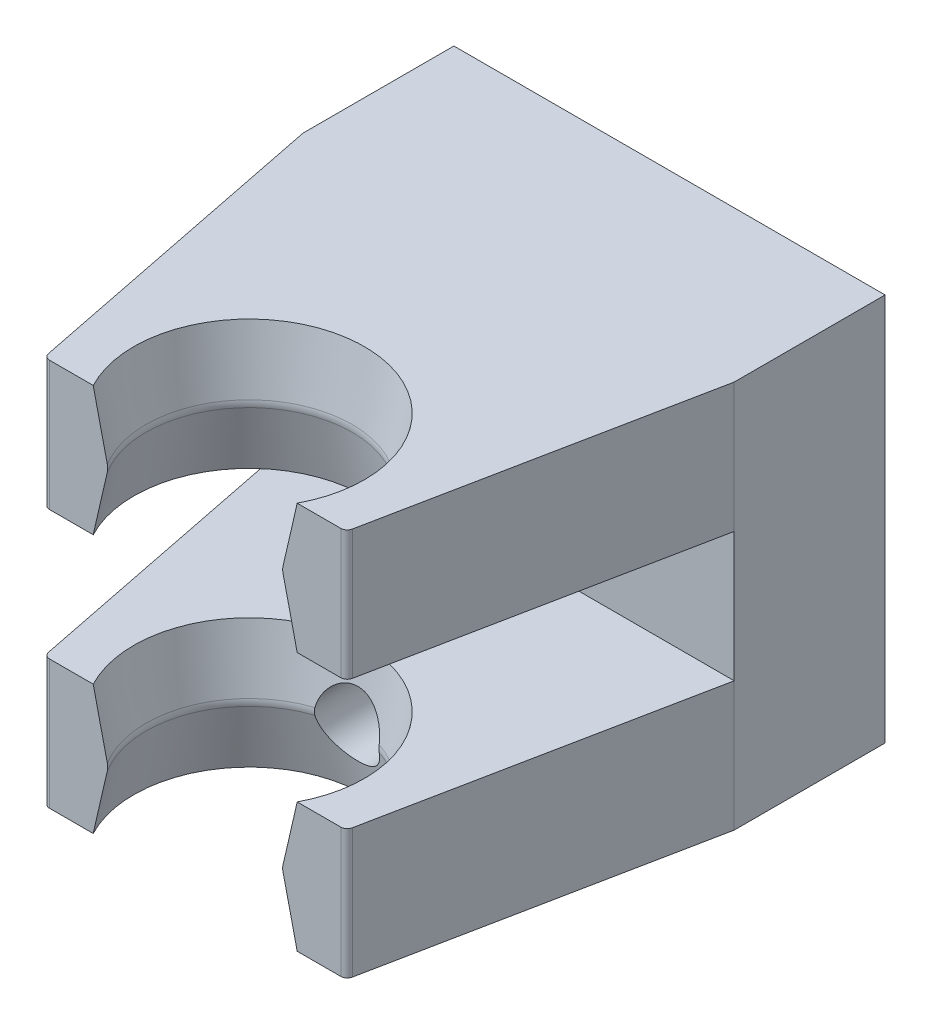
SolidWorks part; units mm, degrees
ref_plane "Front Plane" through (0, 0, 0) normal (0, 0, 1) x (1, 0, 0)
ref_plane "Top Plane" through (0, 0, 0) normal (0, 1, 0) x (1, 0, 0)
ref_plane "Right Plane" through (0, 0, 0) normal (1, 0, 0) x (0, 0, -1)
sketch "Sketch1" plane through (0, 0, 0) normal (0, 0, 1) x (1, 0, 0)
  line L1 (-10, -9) -> (10, -9)
  line L2 (-10, -9) -> (-10, 9)
  line L3 (-10, 9) -> (10, 9)
  line L4 (10, -9) -> (10, 9)
  line L5 (-10, -9) -> (10, 9) construction
  line L6 (-10, 9) -> (10, -9) construction
  point P0 (0, 0)
  dimension "D1" = 18
  dimension "D2" = 20
extrude "Boss-Extrude1" add sketch "Sketch1" along normal blind 7
sketch "Sketch2" plane through (0, 0, 7) normal (0, 0, 1) x (1, 0, 0)
  line L0 (-10, 9) -> (-10, -9) construction
  line L1 (10, -9) -> (-10, -9)
  line L2 (10, -9) -> (10, -3)
  line L3 (10, -3) -> (-10, -3)
  line L4 (-10, -9) -> (-10, -3)
  line L5 (10, -9) -> (10, 9) construction
  line L6 (-10, 9) -> (10, 9)
  line L7 (-10, 9) -> (-10, 3)
  line L8 (-10, 3) -> (10, 3)
  line L9 (10, 9) -> (10, 3)
  dimension "D1" = 6
  dimension "D2" = 6
extrude "Boss-Extrude2" add sketch "Sketch2" along normal blind 15
sketch "Sketch3" plane through (0, -9, 0) normal (0, -1, 0) x (1, 0, 0)
  line L0 (-10, 7) -> (10, 7) construction
  line L1 (-10, 7) -> (10, 7) construction
  line L2 (0, 22) -> (0, 19.5) construction
  line L3 (-10, 22) -> (10, 22) construction
  line L4 (-7, 22) -> (7, 22) construction
  line L5 (-7, 22) -> (-10, 7)
  line L6 (-10, 7) -> (-10, 22)
  line L7 (-10, 22) -> (-7, 22)
  line L8 (7, 22) -> (10, 22)
  line L9 (10, 22) -> (10, 7)
  line L10 (10, 7) -> (7, 22)
  circle A0 centre (0, 19.5) radius 5.35
  point P9 (5.4429, 17)
  point P15 (0, 22)
  dimension "D1" = 10.7
  dimension "D2" = 2.5
  dimension "D3" = 3
extrude "Cut-Extrude1" cut sketch "Sketch3" against normal up to surface (18 mm away) up to face at (0, 9, 11)
ref_axis "Axis1" through (0, -3, 19.5) along (0, -1, 0)
ref_plane "Plane1" through (0, 0, 19.5) normal (0, 0, 1) x (1, 0, 0)
sketch "Sketch4" plane through (0, 0, 19.5) normal (0, 0, 1) x (1, 0, 0)
  line L0 (-5.35, -3) -> (-5.35, -9)
  line L1 (5.35, -9) -> (5.35, -3)
  line L2 (5.35, -9) -> (5.35, -3)
  line L3 (-5.35, -3) -> (-5.35, -9)
  line L4 (-5.35, -3) -> (-4.7814, -5.8431)
  line L5 (-4.7814, -6.1569) -> (-5.35, -9)
  line L6 (-4.75, -6) -> (-5.35, -6) construction
  line L7 (5.35, -9) -> (5.35, -3)
  line L8 (-5.35, -3) -> (-5.35, -9)
  arc A0 (-4.7814, -5.8431) -> (-4.7814, -6.1569) centre (-5.5658, -6) cw
  dimension "D1" = 0.8
  dimension "D2" = 0.6
revolve "Revolve4" add sketch "Sketch4" angle 360 about axis through (0, -3, 19.5) along (0, -1, 0)
sketch "Sketch5" plane through (0, 0, 22) normal (0, 0, 1) x (1, 0, 0)
  line L1 (-7, -9) -> (7, -9)
  line L2 (-7, -9) -> (-7, -3)
  line L3 (-7, -3) -> (7, -3)
  line L4 (7, -9) -> (7, -3)
extrude "Cut-Extrude2" cut sketch "Sketch5" along normal through all
fillet "Fillet1" radius 0.3 6 edges at (7, 6, 22) (-4.73, 6, 22) (4.73, 6, 22) (-7, 6, 22) (-7, -6, 22) (7, -6, 22)
sketch "Sketch6" plane through (0, 0, 7) normal (0, 0, 1) x (1, 0, 0)
  line L0 (-10, 3) -> (-10, -3) construction
  line L1 (-10, 0) -> (10, 0)
  line L2 (-10, 0) -> (-10, 9)
  line L3 (-10, 9) -> (10, 9)
  line L4 (10, 0) -> (10, 9)
extrude "Cut-Extrude3" cut sketch "Sketch6" against normal through all both and the other way through all
mirror "Mirror2" about plane through (-10, 0, 0) normal (0, -1, 0) of bodies 106
sketch "Sketch7" plane through (0, 0, 0) normal (0, 0, -1) x (-1, 0, 0)
  line L0 (-10, -3) -> (10, -3) construction
  line L1 (-10, -3) -> (10, -3) construction
  line L2 (0, -3) -> (0, -9) construction
  line L3 (10, -9) -> (-10, -9) construction
  circle A0 centre (0, -6) radius 1.5
  dimension "D1" = 3
extrude "Cut-Extrude4" cut sketch "Sketch7" against normal through all both and the other way through all
